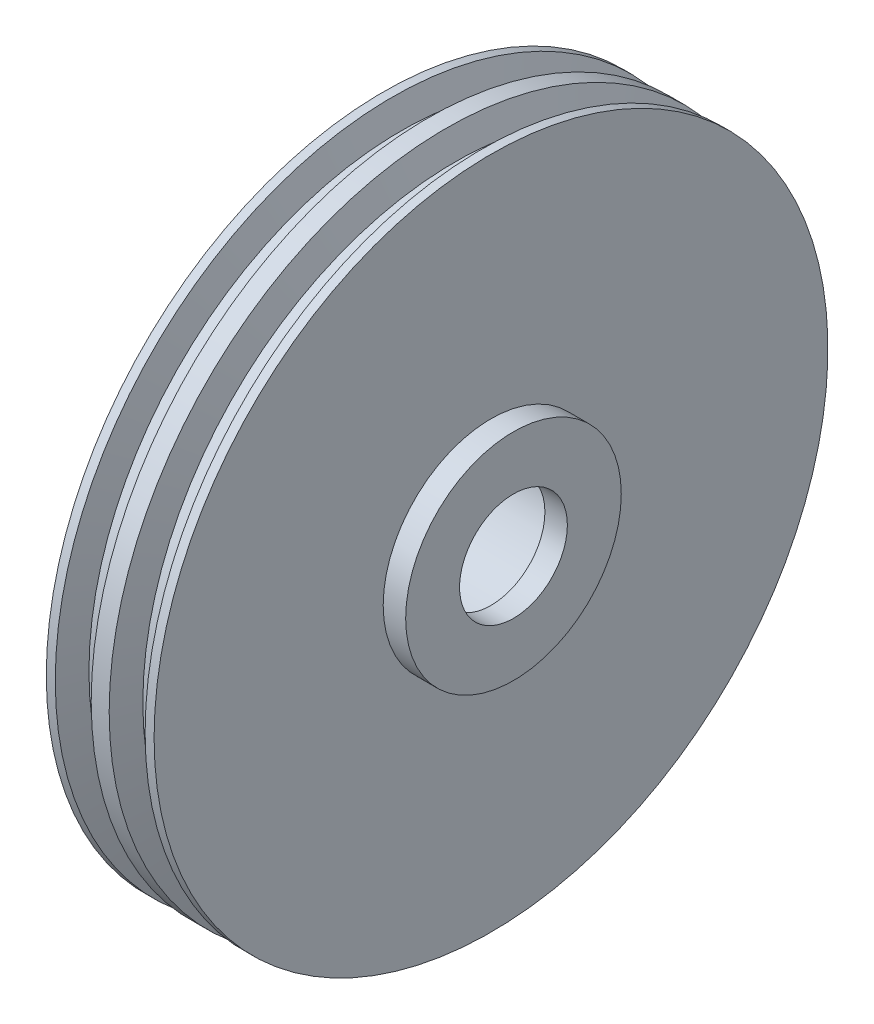
SolidWorks part; units mm, degrees
ref_plane "Front Plane" through (0, 0, 0) normal (0, 0, 1) x (1, 0, 0)
ref_plane "Top Plane" through (0, 0, 0) normal (0, 1, 0) x (1, 0, 0)
ref_plane "Right Plane" through (0, 0, 0) normal (1, 0, 0) x (0, 0, -1)
sketch "Sketch1" plane through (0, 0, 0) normal (0, 0, 1) x (1, 0, 0)
  line L0 (0, 0) -> (210.5852, 0) construction
  line L1 (0, 0) -> (0, 37.5)
  line L2 (0, 37.5) -> (1, 37.5)
  line L3 (1, 37.5) -> (2, 34.7525)
  line L4 (2, 34.7525) -> (4, 34.7525)
  line L5 (4, 34.7525) -> (5, 37.5)
  line L6 (5, 37.5) -> (6, 37.5)
  line L7 (6, 37.5) -> (6, 0)
  line L8 (6, 0) -> (0, 0)
  point P3 (0, 0)
  point P11 (0, 0)
  point P12 (0, 0)
  point P13 (0, 0)
  point P14 (1.3781, 56.8053)
  point P15 (12.0388, 44.6216)
  point P16 (0, 0)
  point P17 (0, 0)
  point P18 (8.4852, 44.5201)
  point P19 (4.8301, 48.3782)
  point P20 (0.9596, 56.6568)
  point P21 (0.4385, 56.6725)
  point P22 (0, 0)
  point P23 (4.119, 56.6937)
  dimension "D1" = 110
  dimension "D2" = 110
  dimension "D3" = 6
  dimension "D4" = 37.5
  dimension "D5" = 1
  dimension "D6" = 2
revolve "Revolve1" add sketch "Sketch1" angle 360 about L0
sketch "Sketch2" plane through (6, 0, 0) normal (1, 0, 0) x (0, 0, -1)
  circle A1 centre (0, 0) radius 9.529
extrude "Cut-Extrude2" cut sketch "Sketch2" against normal blind 62 contours A1
sketch "Sketch3" plane through (6, 0, 0) normal (1, 0, 0) x (0, 0, -1)
  circle A0 centre (0, 0) radius 12
  circle A1 centre (0, 0) radius 6
extrude "Boss-Extrude1" add sketch "Sketch3" along normal blind 2.5
mirror "Mirror1" about plane through (0, 0, 0) normal (1, 0, 0) of bodies 104
